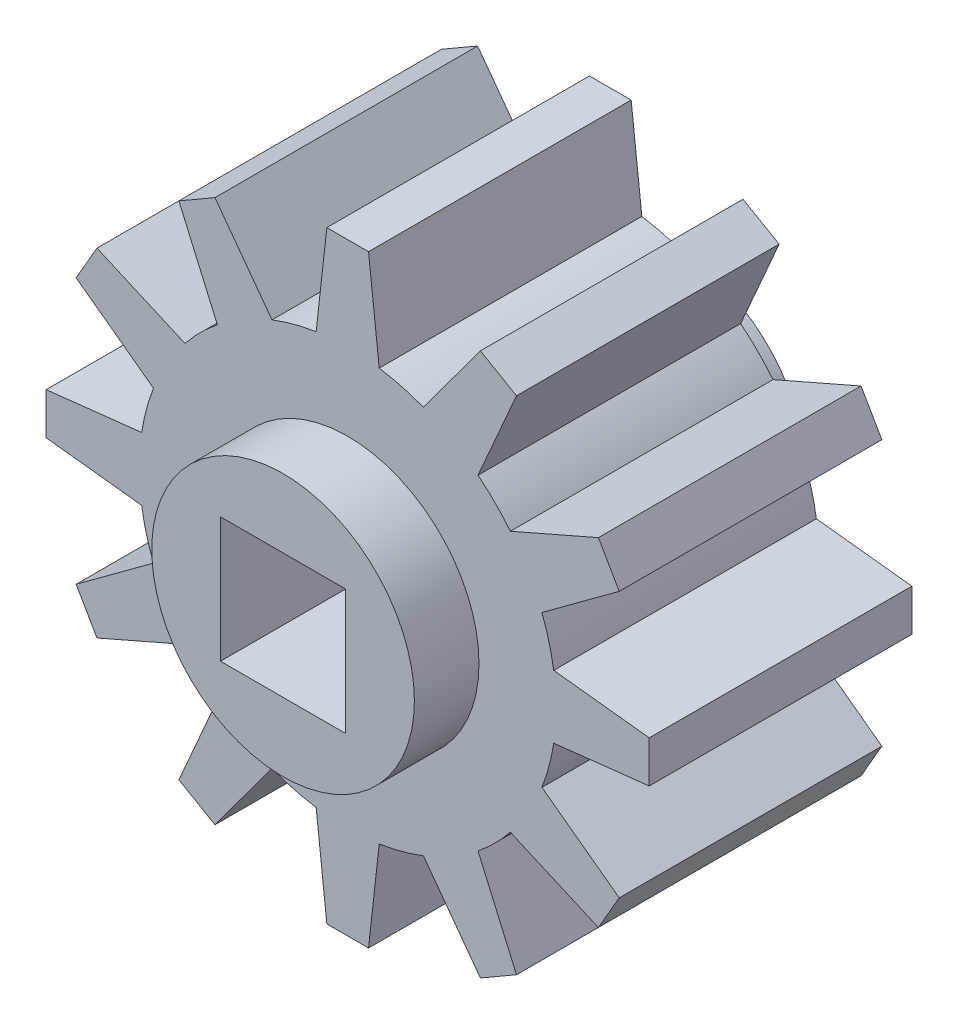
SolidWorks part; units mm, degrees
ref_plane "Front Plane" through (0, 0, 0) normal (0, 0, 1) x (1, 0, 0)
ref_plane "Top Plane" through (0, 0, 0) normal (0, 1, 0) x (1, 0, 0)
ref_plane "Right Plane" through (0, 0, 0) normal (1, 0, 0) x (0, 0, -1)
sketch "Sketch1" plane through (0, 0, 0) normal (0, 0, 1) x (1, 0, 0)
  line L0 (-0.5, 7.2327) -> (0.5, 7.2327)
  line L1 (-1.5, -1.5) -> (1.5, -1.5)
  line L2 (-1.5, -1.5) -> (-1.5, 1.5)
  line L3 (-1.5, 1.5) -> (1.5, 1.5)
  line L4 (1.5, -1.5) -> (1.5, 1.5)
  line L5 (-1.5, -1.5) -> (1.5, 1.5) construction
  line L6 (-1.5, 1.5) -> (1.5, -1.5) construction
  line L7 (-0.75, 5) -> (0.75, 5) construction
  line L8 (-0.5, 7.2327) -> (-0.75, 5)
  line L9 (0.5, 7.2327) -> (0.75, 5)
  line L10 (-0.75, 5) -> (-0.7564, 4.9424)
  line L11 (0.75, 5) -> (0.7564, 4.9424)
  line L12 (3.1834, 6.5137) -> (1.8505, 4.7051)
  line L13 (3.1834, 6.5137) -> (4.0494, 6.0137)
  line L14 (4.0494, 6.0137) -> (3.1495, 3.9551)
  line L15 (1.8505, 4.7051) -> (1.8161, 4.6585)
  line L16 (3.1495, 3.9551) -> (3.1263, 3.9021)
  line L17 (1.8505, 4.7051) -> (3.1495, 3.9551) construction
  line L18 (6.0137, 4.0494) -> (3.9551, 3.1495)
  line L19 (6.0137, 4.0494) -> (6.5137, 3.1834)
  line L20 (6.5137, 3.1834) -> (4.7051, 1.8505)
  line L21 (3.9551, 3.1495) -> (3.9021, 3.1263)
  line L22 (4.7051, 1.8505) -> (4.6585, 1.8161)
  line L23 (3.9551, 3.1495) -> (4.7051, 1.8505) construction
  line L24 (7.2327, 0.5) -> (5, 0.75)
  line L25 (7.2327, 0.5) -> (7.2327, -0.5)
  line L26 (7.2327, -0.5) -> (5, -0.75)
  line L27 (5, 0.75) -> (4.9424, 0.7564)
  line L28 (5, -0.75) -> (4.9424, -0.7564)
  line L29 (5, 0.75) -> (5, -0.75) construction
  line L30 (6.5137, -3.1834) -> (4.7051, -1.8505)
  line L31 (6.5137, -3.1834) -> (6.0137, -4.0494)
  line L32 (6.0137, -4.0494) -> (3.9551, -3.1495)
  line L33 (4.7051, -1.8505) -> (4.6585, -1.8161)
  line L34 (3.9551, -3.1495) -> (3.9021, -3.1263)
  line L35 (4.7051, -1.8505) -> (3.9551, -3.1495) construction
  line L36 (4.0494, -6.0137) -> (3.1495, -3.9551)
  line L37 (4.0494, -6.0137) -> (3.1834, -6.5137)
  line L38 (3.1834, -6.5137) -> (1.8505, -4.7051)
  line L39 (3.1495, -3.9551) -> (3.1263, -3.9021)
  line L40 (1.8505, -4.7051) -> (1.8161, -4.6585)
  line L41 (3.1495, -3.9551) -> (1.8505, -4.7051) construction
  line L42 (0.5, -7.2327) -> (0.75, -5)
  line L43 (0.5, -7.2327) -> (-0.5, -7.2327)
  line L44 (-0.5, -7.2327) -> (-0.75, -5)
  line L45 (0.75, -5) -> (0.7564, -4.9424)
  line L46 (-0.75, -5) -> (-0.7564, -4.9424)
  line L47 (0.75, -5) -> (-0.75, -5) construction
  line L48 (-3.1834, -6.5137) -> (-1.8505, -4.7051)
  line L49 (-3.1834, -6.5137) -> (-4.0494, -6.0137)
  line L50 (-4.0494, -6.0137) -> (-3.1495, -3.9551)
  line L51 (-1.8505, -4.7051) -> (-1.8161, -4.6585)
  line L52 (-3.1495, -3.9551) -> (-3.1263, -3.9021)
  line L53 (-1.8505, -4.7051) -> (-3.1495, -3.9551) construction
  line L54 (-6.0137, -4.0494) -> (-3.9551, -3.1495)
  line L55 (-6.0137, -4.0494) -> (-6.5137, -3.1834)
  line L56 (-6.5137, -3.1834) -> (-4.7051, -1.8505)
  line L57 (-3.9551, -3.1495) -> (-3.9021, -3.1263)
  line L58 (-4.7051, -1.8505) -> (-4.6585, -1.8161)
  line L59 (-3.9551, -3.1495) -> (-4.7051, -1.8505) construction
  line L60 (-7.2327, -0.5) -> (-5, -0.75)
  line L61 (-7.2327, -0.5) -> (-7.2327, 0.5)
  line L62 (-7.2327, 0.5) -> (-5, 0.75)
  line L63 (-5, -0.75) -> (-4.9424, -0.7564)
  line L64 (-5, 0.75) -> (-4.9424, 0.7564)
  line L65 (-5, -0.75) -> (-5, 0.75) construction
  line L66 (-6.5137, 3.1834) -> (-4.7051, 1.8505)
  line L67 (-6.5137, 3.1834) -> (-6.0137, 4.0494)
  line L68 (-6.0137, 4.0494) -> (-3.9551, 3.1495)
  line L69 (-4.7051, 1.8505) -> (-4.6585, 1.8161)
  line L70 (-3.9551, 3.1495) -> (-3.9021, 3.1263)
  line L71 (-4.7051, 1.8505) -> (-3.9551, 3.1495) construction
  line L72 (-4.0494, 6.0137) -> (-3.1495, 3.9551)
  line L73 (-4.0494, 6.0137) -> (-3.1834, 6.5137)
  line L74 (-3.1834, 6.5137) -> (-1.8505, 4.7051)
  line L75 (-3.1495, 3.9551) -> (-3.1263, 3.9021)
  line L76 (-1.8505, 4.7051) -> (-1.8161, 4.6585)
  line L77 (-3.1495, 3.9551) -> (-1.8505, 4.7051) construction
  circle A0 centre (0, 0) radius 7.25 construction
  circle A1 centre (0, 0) radius 5
  point P0 (0, 0)
  point P11 (0, 7.2327)
  point P12 (0, 1.5)
  point P15 (0, 5)
  point P16 (-5.7833, -0.2694)
  point P19 (0, 0)
  point P87 (0, 0)
  dimension "D2" = 14.5
  dimension "D3" = 10
  dimension "D1" = 3
  dimension "D4" = 1
  dimension "D5" = 1.5
  dimension "D6" = 12
extrude "Boss-Extrude1" add sketch "Sketch1" along normal blind 6.3 contours A1 L4 L1 L2 L3 | A1 L64 L62 L61 L60 L63 | A1 L70 L68 L67 L66 L69 | A1 L76 L74 L73 L72 L75 | A1 L11 L9 L0 L8 L10 | A1 L16 L14 L13 L12 L15 | A1 L22 L20 L19 L18 L21 | A1 L28 L26 L25 L24 L27 | A1 L34 L32 L31 L30 L33 | A1 L40 L38 L37 L36 L39 | A1 L46 L44 L43 L42 L45 | A1 L52 L50 L49 L48 L51 | A1 L58 L56 L55 L54 L57
sketch "Sketch2" plane through (0, 0, 6.3) normal (0, 0, 1) x (1, 0, 0)
  line L1 (-1.5, -1.5) -> (1.5, -1.5)
  line L2 (-1.5, -1.5) -> (-1.5, 1.5)
  line L3 (-1.5, 1.5) -> (1.5, 1.5)
  line L4 (1.5, -1.5) -> (1.5, 1.5)
  circle A0 centre (0, 0) radius 3.15
  dimension "D1" = 6.3
extrude "Boss-Extrude2" add sketch "Sketch2" along normal blind 1.55
sketch "Sketch3" plane through (0, 0, 0) normal (0, 0, -1) x (-1, 0, 0)
  line L1 (-1.5, 1.5) -> (1.5, 1.5)
  line L2 (-1.5, 1.5) -> (-1.5, -1.5)
  line L3 (-1.5, -1.5) -> (1.5, -1.5)
  line L4 (1.5, 1.5) -> (1.5, -1.5)
  circle A0 centre (0, 0) radius 3.15
  dimension "D1" = 6.3
extrude "Boss-Extrude3" add sketch "Sketch3" along normal blind 1.55
